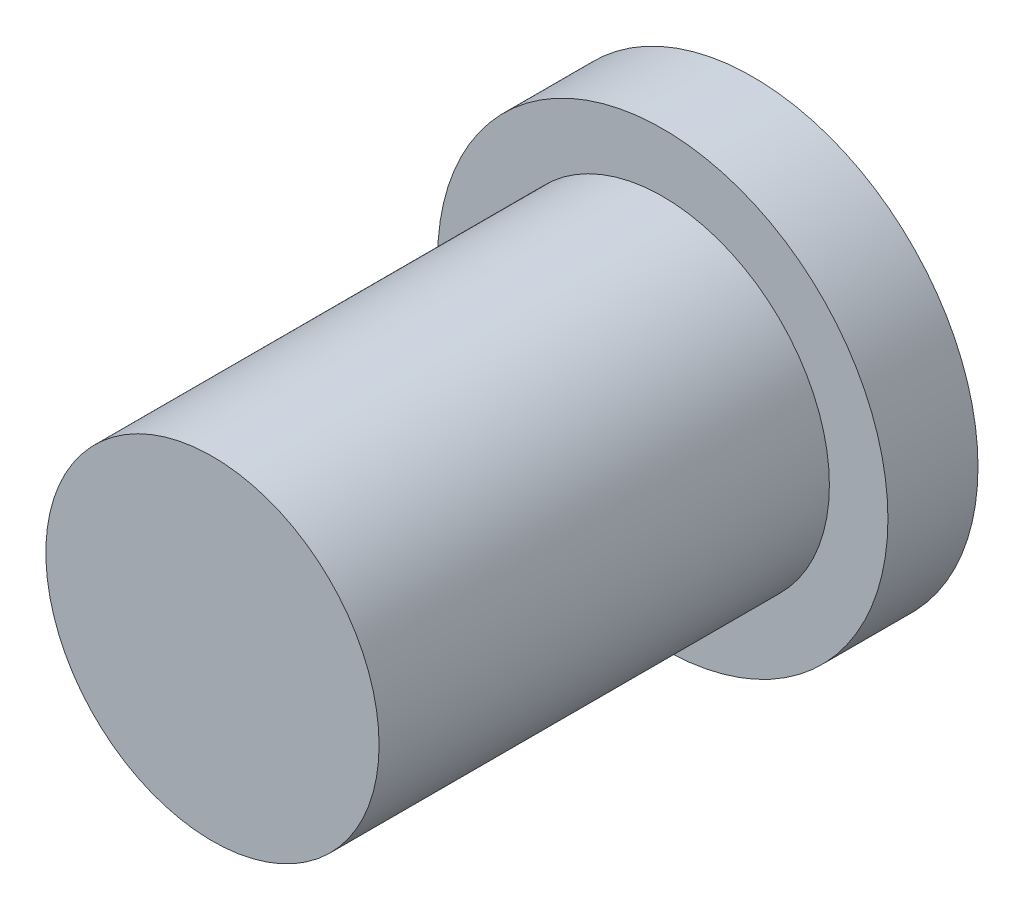
SolidWorks part; units mm, degrees
ref_plane "Front Plane" through (0, 0, 0) normal (0, 0, 1) x (1, 0, 0)
ref_plane "Top Plane" through (0, 0, 0) normal (0, 1, 0) x (1, 0, 0)
ref_plane "Right Plane" through (0, 0, 0) normal (1, 0, 0) x (0, 0, -1)
sketch "Sketch1" plane through (0, 0, 0) normal (0, 0, 1) x (1, 0, 0)
  circle A0 centre (0, 0) radius 3.7
  dimension "D1" = 7.4
extrude "Boss-Extrude1" add sketch "Sketch1" along normal blind 10
sketch "Sketch2" plane through (0, 0, 0) normal (0, 0, -1) x (-1, 0, 0)
  circle A0 centre (0, 0) radius 5
  dimension "D1" = 10
extrude "Boss-Extrude2" add sketch "Sketch2" along normal blind 2
